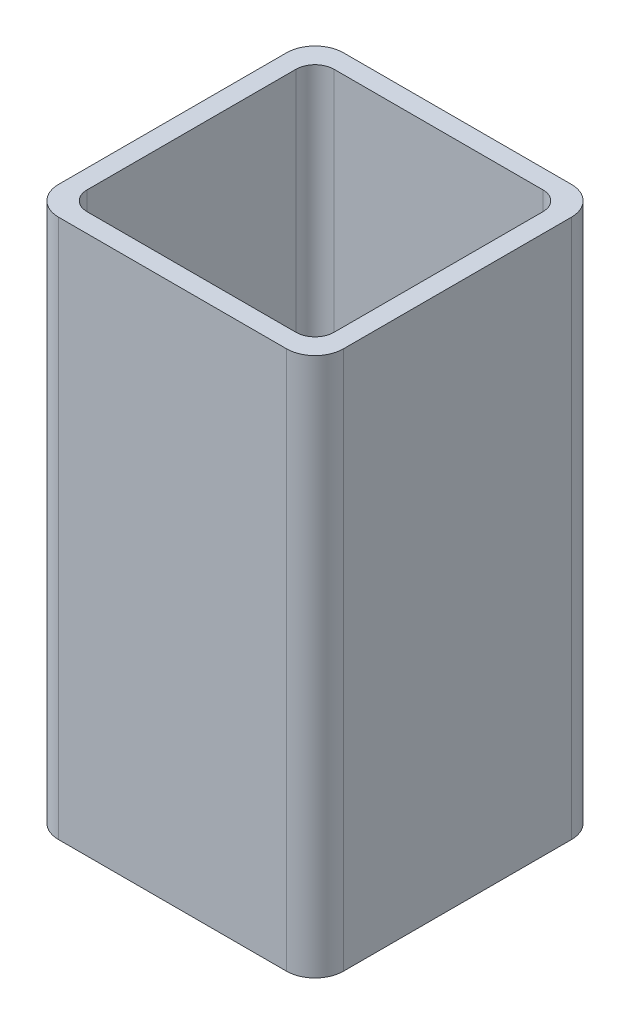
SolidWorks part; units mm, degrees
material "AISI 1020"
ref_plane "Спереди" through (0, 0, 0) normal (0, 0, 1) x (1, 0, 0)
ref_plane "Сверху" through (0, 0, 0) normal (0, 1, 0) x (1, 0, 0)
ref_plane "Справа" through (0, 0, 0) normal (1, 0, 0) x (0, 0, -1)
sketch "Эскиз1" plane through (0, 0, 0) normal (0, 1, 0) x (1, 0, 0)
  line L0 (0, -12) -> (0, 12) construction
  point P2 (0, 0)
  line B0 (-27, 15) -> (-3, 15)
  line B1 (-30, 12) -> (-30, -12)
  line B2 (-27, -15) -> (-3, -15)
  line B3 (0, 12) -> (0, -12)
  line B4 (-26, 13) -> (-4, 13)
  line B5 (-28, 11) -> (-28, -11)
  line B6 (-26, -13) -> (-4, -13)
  line B7 (-2, 11) -> (-2, -11)
  arc B8 (-30, -12) -> (-27, -15) centre (-27, -12) ccw
  arc B9 (-3, -15) -> (0, -12) centre (-3, -12) ccw
  arc B10 (-3, 15) -> (0, 12) centre (-3, 12) cw
  arc B11 (-27, 15) -> (-30, 12) centre (-27, 12) ccw
  arc B12 (-28, -11) -> (-26, -13) centre (-26, -11) ccw
  arc B13 (-4, -13) -> (-2, -11) centre (-4, -11) ccw
  arc B14 (-4, 13) -> (-2, 11) centre (-4, 11) cw
  arc B15 (-26, 13) -> (-28, 11) centre (-26, 11) ccw
sketch_block_instance "Блок-30х30х2-1"
sketch_block "Блок-30х30х2" parameters "D3"=3, "D4"=2, "D1"=30, "D2"=2
extrude "Бобышка-Вытянуть1" add sketch "Эскиз1" against normal up to surface (56.7738 mm away)
